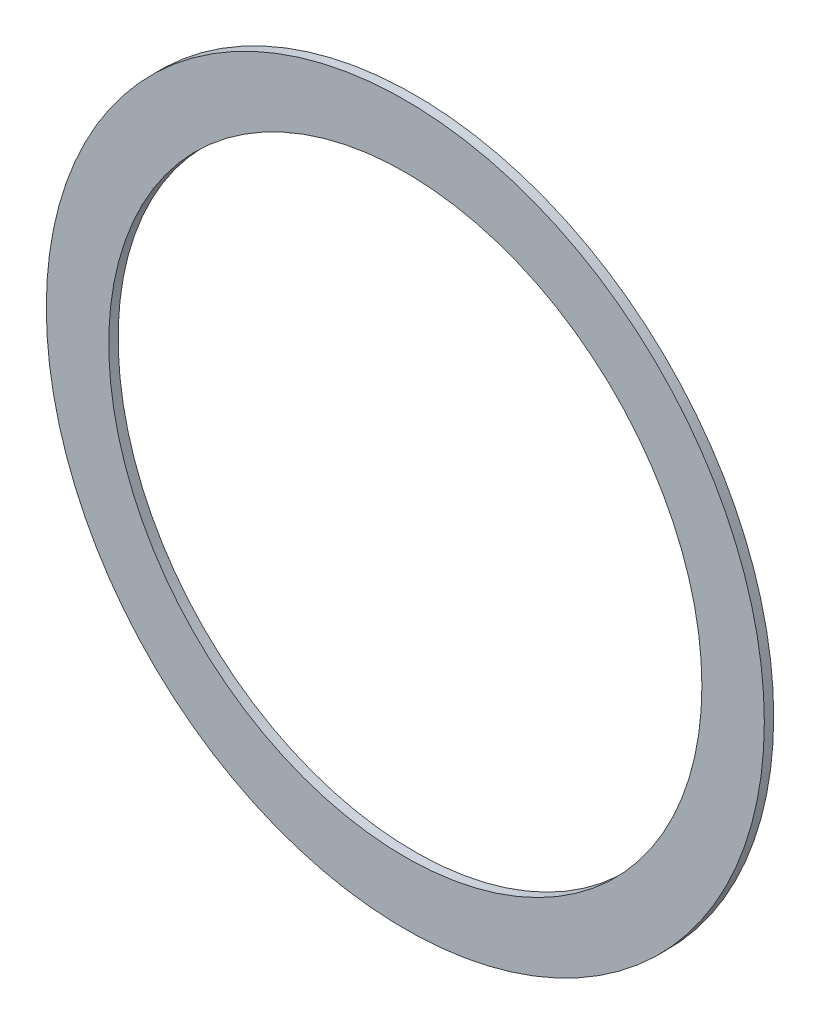
SolidWorks part; units mm, degrees
ref_plane "Alzado" through (0, 0, 0) normal (0, 0, 1) x (1, 0, 0)
ref_plane "Planta" through (0, 0, 0) normal (0, 1, 0) x (1, 0, 0)
ref_plane "Vista lateral" through (0, 0, 0) normal (1, 0, 0) x (0, 0, -1)
sketch "Croquis1" plane through (0, 0, 0) normal (0, 0, 1) x (1, 0, 0)
  circle A0 centre (0, 0) radius 115
  circle A1 centre (0, 0) radius 95
  dimension "D1" = 190
  dimension "D2" = 20
extrude "Saliente-Extruir1" add sketch "Croquis1" along normal blind 3
